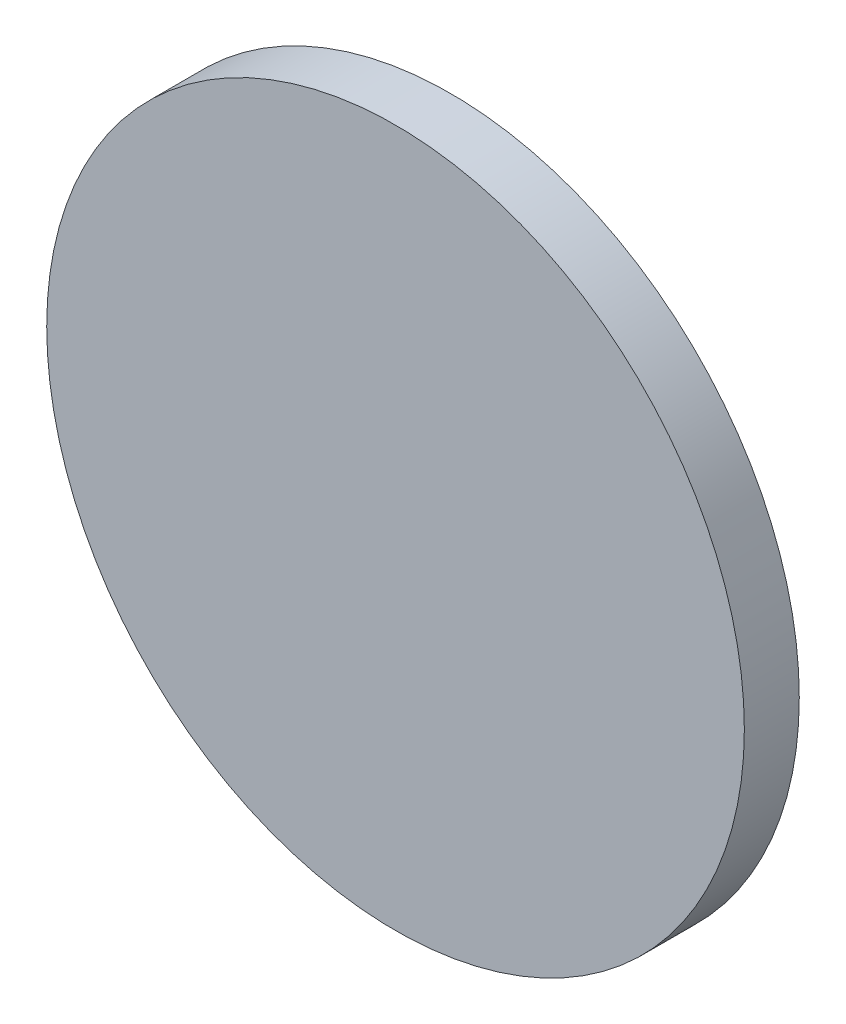
SolidWorks part; units mm, degrees
ref_plane "前视基准面" through (0, 0, 0) normal (0, 0, 1) x (1, 0, 0)
ref_plane "上视基准面" through (0, 0, 0) normal (0, 1, 0) x (1, 0, 0)
ref_plane "右视基准面" through (0, 0, 0) normal (1, 0, 0) x (0, 0, -1)
sketch "草图1" plane through (0, 0, 0) normal (0, 0, 1) x (1, 0, 0)
  circle A0 centre (0, 0) radius 25.4
  dimension "D1" = 50.8
extrude "凸台-拉伸1" add sketch "草图1" along normal blind 4 contours A0
